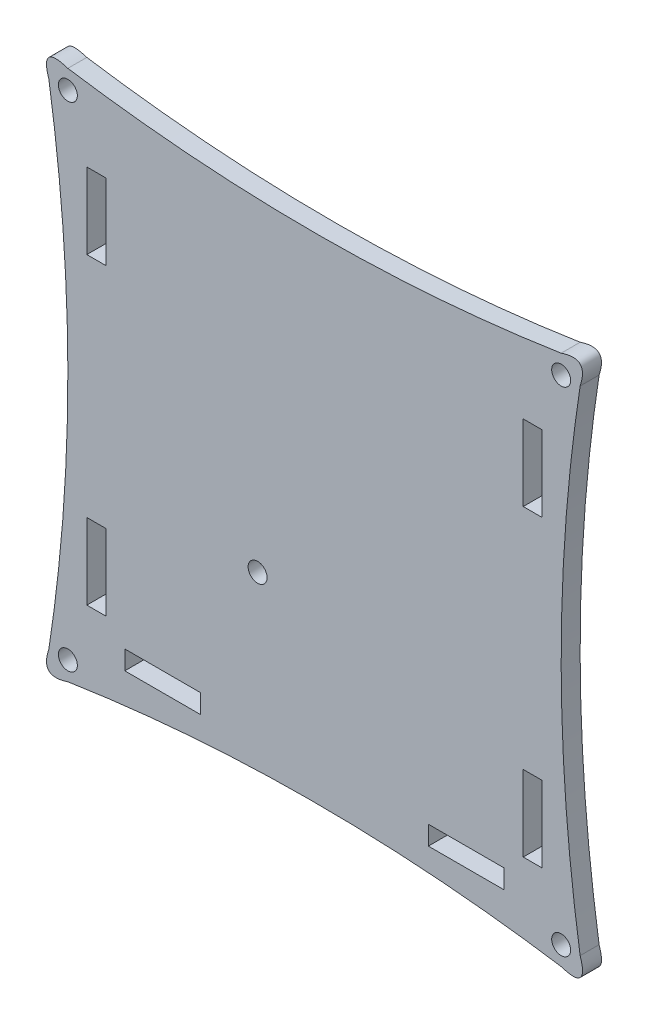
SolidWorks part; units mm, degrees
ref_plane "Front Plane" through (0, 0, 0) normal (0, 0, 1) x (1, 0, 0)
ref_plane "Top Plane" through (0, 0, 0) normal (0, 1, 0) x (1, 0, 0)
ref_plane "Right Plane" through (0, 0, 0) normal (1, 0, 0) x (0, 0, -1)
sketch "Sketch1" plane through (0, 0, 0) normal (0, 0, 1) x (1, 0, 0)
  line L0 (12.7, 50.8) -> (19.05, 50.8)
  line L1 (25.4, 19.05) -> (50.8, 19.05)
  line L2 (12.7, 152.4) -> (12.7, 127)
  line L3 (25.4, 12.7) -> (50.8, 12.7)
  line L4 (19.05, 152.4) -> (19.05, 127)
  line L5 (12.7, 25.4) -> (19.05, 25.4)
  line L6 (12.7, 152.4) -> (19.05, 152.4)
  line L7 (12.7, 127) -> (19.05, 127)
  line L8 (165.1, 152.4) -> (158.75, 152.4)
  line L9 (127, 19.05) -> (152.4, 19.05)
  line L10 (19.05, 50.8) -> (19.05, 25.4)
  line L11 (127, 12.7) -> (152.4, 12.7)
  line L12 (12.7, 50.8) -> (12.7, 25.4)
  line L13 (165.1, 127) -> (158.75, 127)
  line L14 (158.75, 50.8) -> (165.1, 50.8)
  line L15 (158.75, 25.4) -> (165.1, 25.4)
  line L16 (165.1, 152.4) -> (165.1, 127)
  line L17 (158.75, 152.4) -> (158.75, 127)
  line L18 (158.75, 50.8) -> (158.75, 25.4)
  line L19 (165.1, 50.8) -> (165.1, 25.4)
  line L20 (25.4, 12.7) -> (25.4, 19.05)
  line L21 (50.8, 19.05) -> (50.8, 12.7)
  line L22 (152.4, 19.05) -> (152.4, 12.7)
  line L23 (127, 19.05) -> (127, 12.7)
  spline S0 degree 2 poles (0, 171.45) (12.7, 88.9) (0, 6.35) knots 0 0 0 1 1 1
  spline S1 degree 2 poles (0, 171.45) (-3.175, 180.975) (6.35, 177.8) knots 0 0 0 1 1 1
  spline S2 degree 2 poles (6.35, 177.8) (88.9, 165.1) (171.45, 177.8) knots 0 0 0 1 1 1
  spline S3 degree 2 poles (171.45, 177.8) (180.975, 180.975) (177.8, 171.45) knots 0 0 0 1 1 1
  spline S4 degree 2 poles (177.8, 171.45) (165.1, 88.9) (177.8, 6.35) knots 0 0 0 1 1 1
  spline S5 degree 2 poles (177.8, 6.35) (180.975, -3.175) (171.45, 0) knots 0 0 0 1 1 1
  spline S6 degree 2 poles (0, 6.35) (-3.175, -3.175) (6.35, 0) knots 0 0 0 1 1 1
  spline S7 degree 2 poles (6.35, 0) (88.9, 12.7) (171.45, 0) knots 0 0 0 1 1 1
extrude "Boss-Extrude1" add sketch "Sketch1" along normal blind 6.35
sketch "Sketch2" plane through (0, 0, 6.35) normal (0, 0, 1) x (1, 0, 0)
  circle A0 centre (69.85, 63.5) radius 3.175
extrude "Cut-Extrude2" cut sketch "Sketch2" against normal blind 6.35
sketch "Sketch3" plane through (0, 0, 6.35) normal (0, 0, 1) x (1, 0, 0)
  circle A0 centre (6.35, 6.35) radius 3.175
  circle A1 centre (171.45, 6.35) radius 3.175
  circle A2 centre (6.35, 171.45) radius 3.175
  circle A3 centre (171.45, 171.45) radius 3.175
extrude "Cut-Extrude3" cut sketch "Sketch3" against normal blind 6.35
